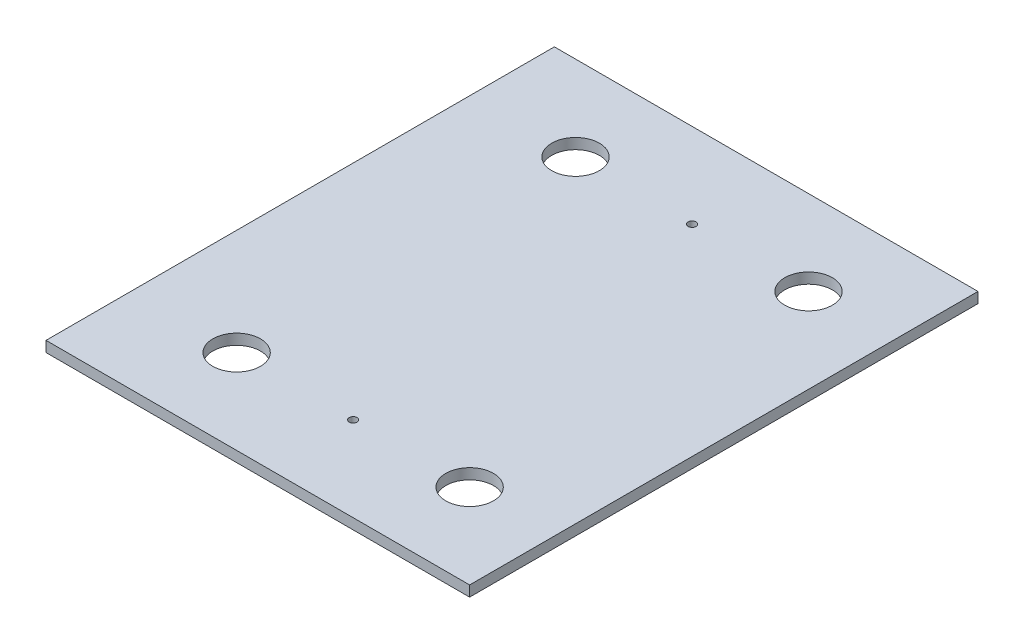
SolidWorks part; units mm, degrees
ref_plane "Front Plane" through (0, 0, 0) normal (0, 0, 1) x (1, 0, 0)
ref_plane "Top Plane" through (0, 0, 0) normal (0, 1, 0) x (1, 0, 0)
ref_plane "Right Plane" through (0, 0, 0) normal (1, 0, 0) x (0, 0, -1)
sketch "Sketch1" plane through (0, 0, 0) normal (0, 1, 0) x (1, 0, 0)
  line L0 (63.5, 254) -> (203.2, 254) construction
  line L1 (0, 0) -> (254, 0)
  line L2 (0, 0) -> (0, 304.8)
  line L3 (0, 304.8) -> (254, 304.8)
  line L4 (254, 0) -> (254, 304.8)
  line L5 (63.5, 50.8) -> (203.2, 50.8) construction
  circle A0 centre (63.5, 50.8) radius 14.2875
  circle A1 centre (203.2, 50.8) radius 14.2875
  circle A2 centre (63.5, 254) radius 14.2875
  circle A3 centre (203.2, 254) radius 14.2875
  circle A4 centre (63.5, 50.8) radius 50.8 construction
  circle A5 centre (203.2, 50.8) radius 50.8 construction
  circle A6 centre (203.2, 254) radius 50.8 construction
  circle A7 centre (63.5, 254) radius 50.8 construction
  circle A8 centre (133.35, 254) radius 2.3813
  circle A9 centre (133.35, 50.8) radius 2.3813
  point P17 (133.35, 254)
  dimension "D1" = 28.575
  dimension "D4" = 101.6
  dimension "D5" = 101.6
  dimension "D6" = 4.7625
  dimension "D2" = 254
  dimension "D3" = 139.7
extrude "Boss-Extrude1" add sketch "Sketch1" along normal blind 6.35
